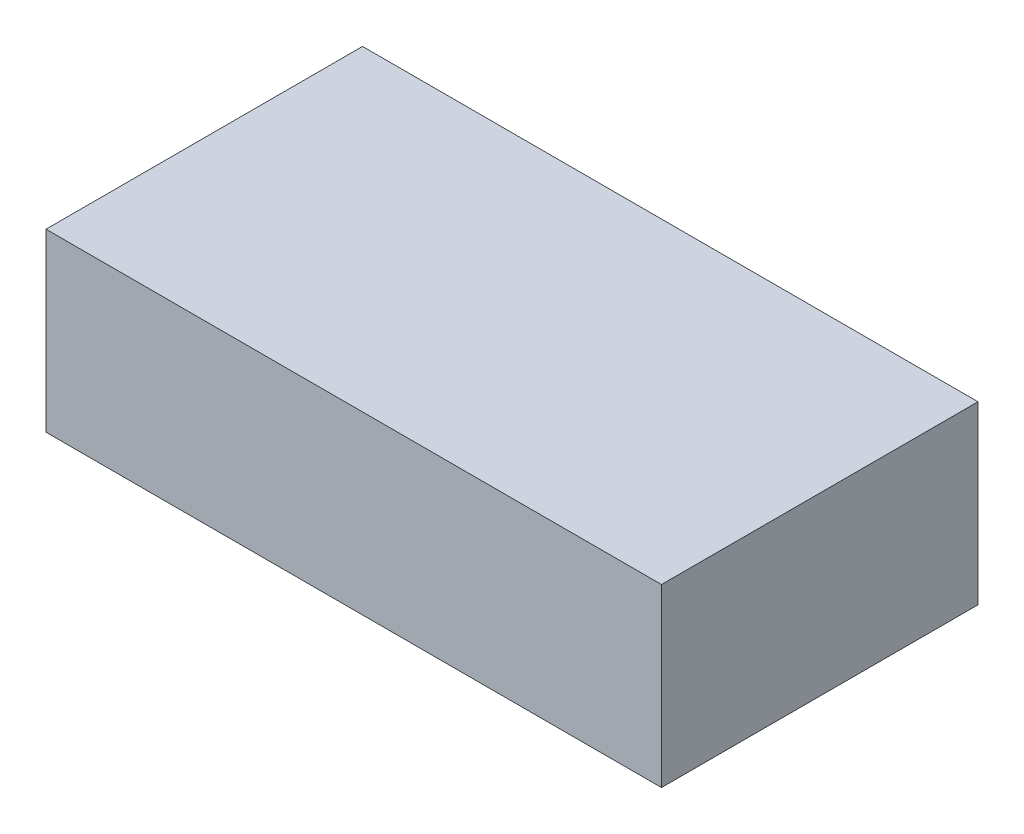
SolidWorks part; units mm, degrees
ref_plane "Front Plane" through (0, 0, 0) normal (0, 0, 1) x (1, 0, 0)
ref_plane "Top Plane" through (0, 0, 0) normal (0, 1, 0) x (1, 0, 0)
ref_plane "Right Plane" through (0, 0, 0) normal (1, 0, 0) x (0, 0, -1)
sketch "Sketch1" plane through (0, 0, 0) normal (0, 1, 0) x (1, 0, 0)
  line L1 (-17.5, 9) -> (17.5, 9)
  line L2 (-17.5, 9) -> (-17.5, -9)
  line L3 (-17.5, -9) -> (17.5, -9)
  line L4 (17.5, 9) -> (17.5, -9)
  line L5 (-17.5, 9) -> (17.5, -9) construction
  line L6 (-17.5, -9) -> (17.5, 9) construction
  point P0 (0, 0)
  dimension "D1" = 35
  dimension "D2" = 18
extrude "Boss-Extrude1" add sketch "Sketch1" along normal blind 10
